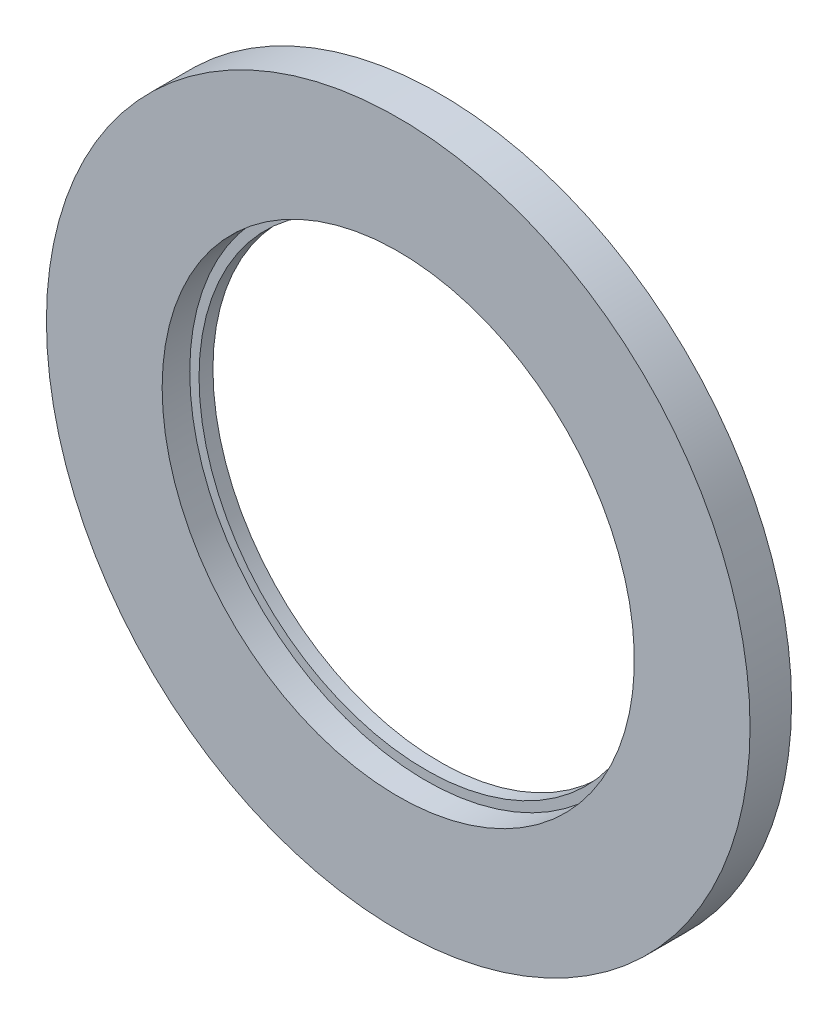
SolidWorks part; units mm, degrees
material "6061 Alloy"
ref_plane "Front Plane" through (0, 0, 0) normal (0, 0, 1) x (1, 0, 0)
ref_plane "Top Plane" through (0, 0, 0) normal (0, 1, 0) x (1, 0, 0)
ref_plane "Right Plane" through (0, 0, 0) normal (1, 0, 0) x (0, 0, -1)
ref_plane "Plane1" through (0, 0, 0) normal (0, -1, 0) x (1, 0, 0)
sketch "Sketch1" plane through (0, 0, 0) normal (0, -1, 0) x (1, 0, 0)
  line L0 (48.9, 0) -> (75.85, 0)
  line L1 (75.85, 0) -> (75.85, 8.951)
  line L2 (75.85, 8.951) -> (50.9, 8.951)
  line L3 (50.9, 8.951) -> (50.9, 3)
  line L4 (50.9, 3) -> (48.9, 3)
  line L5 (48.9, 3) -> (48.9, 0)
  line L6 (0, 10) -> (0, 0) construction
  dimension "D1" = 3
  dimension "D2" = 8.951
revolve "Revolve1" add sketch "Sketch1" angle 360 about L6
